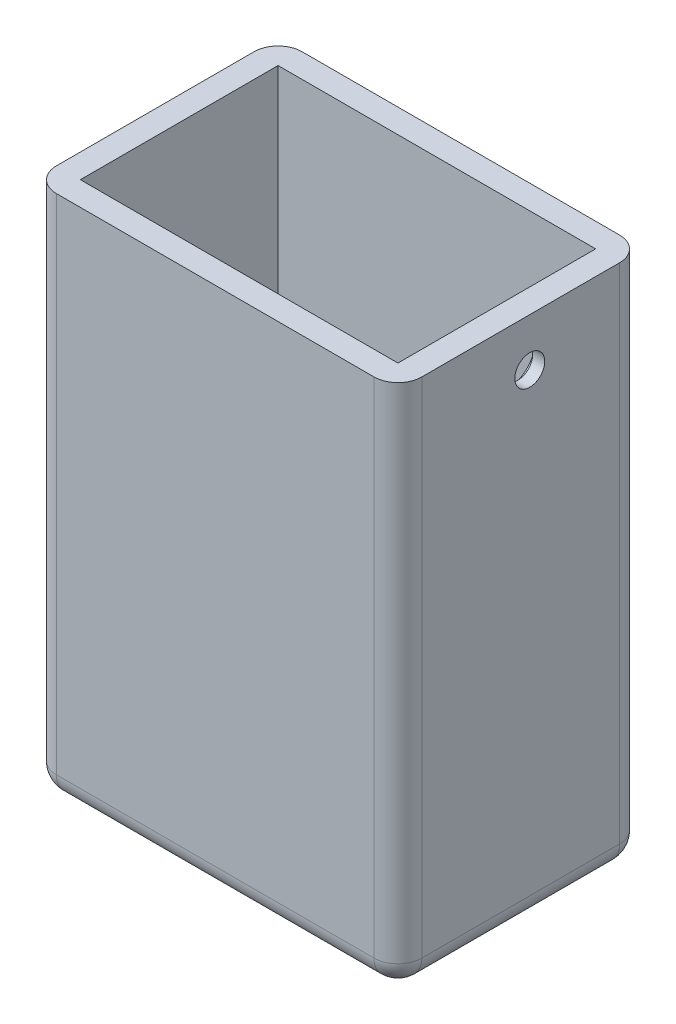
SolidWorks part; units mm, degrees
ref_plane "Plano frontal" through (0, 0, 0) normal (0, 0, 1) x (1, 0, 0)
ref_plane "Plano superior" through (0, 0, 0) normal (0, 1, 0) x (1, 0, 0)
ref_plane "Plano direito" through (0, 0, 0) normal (1, 0, 0) x (0, 0, -1)
sketch "Esboço1" plane through (0, 0, 0) normal (0, 0, 1) x (1, 0, 0)
  line L0 (-42.734, 23.5371) -> (18.266, 23.5371)
  line L1 (-38.734, 19.5371) -> (14.266, 19.5371)
  line L2 (-38.734, 19.5371) -> (-38.734, -64.4629)
  line L3 (-38.734, -64.4629) -> (14.266, -64.4629)
  line L4 (14.266, 19.5371) -> (14.266, -64.4629)
  line L5 (18.266, 23.5371) -> (18.266, -68.4629)
  line L6 (-42.734, -68.4629) -> (18.266, -68.4629)
  line L7 (-42.734, 23.5371) -> (-42.734, -68.4629)
  dimension "D1" = 53
  dimension "D2" = 84
  dimension "D3" = 4
extrude "Ressalto-extrusão2" add sketch "Esboço1" against normal blind 33 contours L5 L6 L7 L0
sketch "Esboço5" plane through (0, 0, 0) normal (0, 0, 1) x (1, 0, 0)
  line L1 (-42.734, -68.4629) -> (18.266, -68.4629)
  line L2 (-42.734, -68.4629) -> (-42.734, 23.5371)
  line L3 (-42.734, 23.5371) -> (18.266, 23.5371)
  line L4 (18.266, -68.4629) -> (18.266, 23.5371)
extrude "Ressalto-extrusão4" add sketch "Esboço5" along normal blind 4
sketch "Esboço6" plane through (18.266, 0, 0) normal (1, 0, 0) x (0, 0, -1)
  line L0 (33, 23.5371) -> (-4, 23.5371) construction
  line L1 (33, -68.4629) -> (33, 23.5371) construction
  circle A0 centre (18, 11.5371) radius 2.5
  dimension "D1" = 5
  dimension "D2" = 12
  dimension "D3" = 15
extrude "Corte-extrusão4" cut sketch "Esboço6" against normal blind 4
sketch "Esboço7" plane through (14.266, 0, 0) normal (-1, 0, 0) x (0, 0, 1)
  line L0 (-18, 8.3701) -> (-18, 14.8499) construction
  line L1 (-21, 11.5371) -> (-16, 11.5371) construction
  line L2 (-11.1, 10.2871) -> (-13.0819, 10.2871)
  line L3 (-24.9, 12.7871) -> (-22.9181, 12.7871)
  line L4 (-25, 12.6871) -> (-25, 10.3871)
  line L5 (-24.9, 10.2871) -> (-22.9181, 10.2871)
  line L6 (-11, 12.6871) -> (-11, 10.3871)
  line L7 (-11.1, 12.7871) -> (-13.0819, 12.7871)
  arc A0 (-22.8216, 10.2136) -> (-13.1784, 10.2136) centre (-18, 11.5371) ccw
  circle A1 centre (-18, 11.5371) radius 2.5 construction
  arc A2 (-13.1784, 12.8607) -> (-22.8216, 12.8607) centre (-18, 11.5371) ccw
  arc A3 (-22.9181, 12.7871) -> (-22.8216, 12.8607) centre (-22.9181, 12.8871) ccw
  arc A4 (-22.9181, 10.2871) -> (-22.8216, 10.2136) centre (-22.9181, 10.1871) cw
  arc A5 (-13.0819, 10.2871) -> (-13.1784, 10.2136) centre (-13.0819, 10.1871) ccw
  arc A6 (-13.0819, 12.7871) -> (-13.1784, 12.8607) centre (-13.0819, 12.8871) cw
  arc A7 (-11.1, 10.2871) -> (-11, 10.3871) centre (-11.1, 10.3871) ccw
  arc A8 (-11, 12.6871) -> (-11.1, 12.7871) centre (-11.1, 12.6871) ccw
  arc A9 (-25, 10.3871) -> (-24.9, 10.2871) centre (-24.9, 10.3871) ccw
  arc A10 (-24.9, 12.7871) -> (-25, 12.6871) centre (-24.9, 12.6871) ccw
  point P17 (-22.8412, 12.7871)
  point P20 (-22.8412, 10.2871)
  point P23 (-13.1588, 10.2871)
  point P26 (-13.1588, 12.7871)
  point P29 (-11, 10.2871)
  point P32 (-11, 12.7871)
  point P35 (-25, 10.2871)
  point P38 (-25, 12.7871)
  dimension "D1" = 10
  dimension "D3" = 0.1
  dimension "D2" = 2.5
  dimension "D4" = 1.25
  dimension "D5" = 7
extrude "Corte-extrusão5" cut sketch "Esboço7" against normal blind 2
sketch "Esboço8" plane through (0, 0, -33) normal (0, 0, -1) x (-1, 0, 0)
  line L4 (42.734, -68.4629) -> (42.734, 23.5371)
  line L5 (42.734, 23.5371) -> (-18.266, 23.5371)
  line L6 (-18.266, 23.5371) -> (-18.266, -68.4629)
  line L7 (-18.266, -68.4629) -> (42.734, -68.4629)
  line L8 (42.734, -68.4629) -> (42.734, 23.5371)
  line L9 (42.734, 23.5371) -> (-18.266, 23.5371)
  line L10 (-18.266, 23.5371) -> (-18.266, -68.4629)
  line L11 (-18.266, -68.4629) -> (42.734, -68.4629)
  dimension "D1" = 0
extrude "Ressalto-extrusão5" add sketch "Esboço8" along normal blind 4
sketch "Esboço9" plane through (0, 23.5371, 0) normal (0, 1, 0) x (1, 0, 0)
  line L4 (-42.734, 37) -> (-42.734, -4)
  line L5 (-42.734, -4) -> (18.266, -4)
  line L6 (18.266, -4) -> (18.266, 37)
  line L7 (18.266, 37) -> (-42.734, 37)
  line L8 (-42.734, 37) -> (-42.734, -4)
  line L9 (-42.734, -4) -> (18.266, -4)
  line L10 (18.266, -4) -> (18.266, 37)
  line L11 (18.266, 37) -> (-42.734, 37)
  dimension "D1" = 0
extrude "Corte-extrusão6" cut sketch "Esboço9" against normal blind 4
fillet "Filete1" radius 4 8 edges at (-12.234, -68.4629, -37) (-12.234, -68.4629, 4) (18.266, -68.4629, -16.5) (18.266, -24.4629, 4) (18.266, -24.4629, -37) (-42.734, -24.4629, 4) (-42.734, -68.4629, -16.5) (-42.734, -24.4629, -37)
